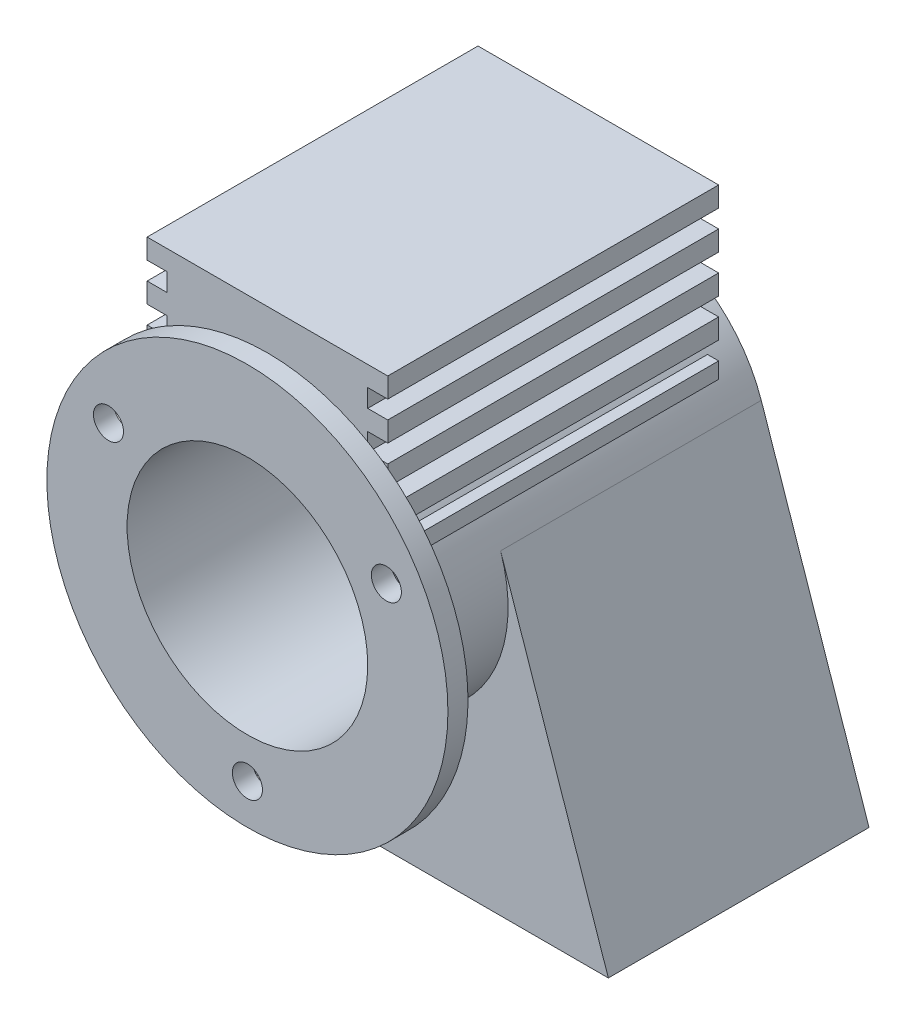
SolidWorks part; units mm, degrees
ref_plane "Front Plane" through (0, 0, 0) normal (0, 0, 1) x (1, 0, 0)
ref_plane "Top Plane" through (0, 0, 0) normal (0, 1, 0) x (1, 0, 0)
ref_plane "Right Plane" through (0, 0, 0) normal (1, 0, 0) x (0, 0, -1)
sketch "Sketch1" plane through (0, 0, 0) normal (0, 0, 1) x (1, 0, 0)
  line L0 (-6, -6.75) -> (6, -6.75)
  line L1 (-6, -6.75) -> (-3.3126, 1.1298)
  line L2 (6, -6.75) -> (3.3126, 1.1298)
  circle A0 centre (0, 0) radius 0.75
  arc A1 (3.3126, 1.1298) -> (-3.3126, 1.1298) centre (0, 0) ccw
  point P6 (0, -6.75)
  dimension "D1" = 1.5
  dimension "D2" = 7
  dimension "D3" = 12
  dimension "D4" = 6.75
extrude "Boss-Extrude1" add sketch "Sketch1" against normal blind 6.5
sketch "Sketch6" plane through (0, 0, 0) normal (0, 0, 1) x (1, 0, 0)
  circle A0 centre (0, 0) radius 3.5
  dimension "D1" = 7
extrude "Boss-Extrude4" add sketch "Sketch6" along normal blind 2.5
sketch "Sketch7" plane through (0, 0, 2.5) normal (0, 0, 1) x (1, 0, 0)
  circle A0 centre (0, 0) radius 5
  dimension "D1" = 10
extrude "Boss-Extrude5" add sketch "Sketch7" along normal blind 0.5
sketch "Sketch8" plane through (0, 0, 3) normal (0, 0, 1) x (1, 0, 0)
  circle A0 centre (0, 0) radius 0.75
  dimension "D1" = 1.5
extrude "Cut-Extrude1" cut sketch "Sketch8" against normal up to surface (3 mm away) up to face at (0, -3.9676, 0)
sketch "Sketch10" plane through (0, 0, 0) normal (0, 0, 1) x (1, 0, 0)
  line L1 (-3, 6) -> (3, 6)
  line L2 (-3, 6) -> (-3, 5.5)
  line L3 (-3, 1.7) -> (3, 1.7)
  line L4 (3, 6) -> (3, 5.5)
  line L8 (-3, 5.05) -> (-3, 4.55)
  line L9 (-3, 5.5) -> (-2.5, 5.5)
  line L10 (-3, 5.05) -> (-2.5, 5.05)
  line L11 (-2.5, 5.5) -> (-2.5, 5.05)
  line L12 (-3, 4.1) -> (-3, 3.6)
  line L13 (-3, 4.55) -> (-2.5, 4.55)
  line L14 (-3, 4.1) -> (-2.5, 4.1)
  line L15 (-2.5, 4.55) -> (-2.5, 4.1)
  line L16 (-3, 3.15) -> (-3, 2.65)
  line L17 (-3, 3.6) -> (-2.5, 3.6)
  line L18 (-3, 3.15) -> (-2.5, 3.15)
  line L19 (-2.5, 3.6) -> (-2.5, 3.15)
  line L20 (3, 5.05) -> (3, 4.55)
  line L21 (3, 5.5) -> (2.5, 5.5)
  line L22 (3, 5.05) -> (2.5, 5.05)
  line L23 (2.5, 5.5) -> (2.5, 5.05)
  line L24 (3, 4.1) -> (3, 3.6)
  line L25 (3, 4.55) -> (2.5, 4.55)
  line L26 (3, 4.1) -> (2.5, 4.1)
  line L27 (2.5, 4.55) -> (2.5, 4.1)
  line L28 (3, 3.15) -> (3, 2.65)
  line L29 (3, 3.6) -> (2.5, 3.6)
  line L30 (3, 3.15) -> (2.5, 3.15)
  line L31 (2.5, 3.6) -> (2.5, 3.15)
  line L32 (-3, 2.2) -> (-3, 1.7)
  line L33 (-3, 2.2) -> (-2.5, 2.2)
  line L34 (-3, 2.65) -> (-2.5, 2.65)
  line L35 (-2.5, 2.2) -> (-2.5, 2.65)
  line L36 (3, 2.2) -> (3, 1.7)
  line L37 (3, 2.65) -> (2.5, 2.65)
  line L38 (3, 2.2) -> (2.5, 2.2)
  line L39 (2.5, 2.65) -> (2.5, 2.2)
  point P4 (0, 1.7)
  point P5 (2.4988, 1.9984)
  dimension "D1" = 6
  dimension "D2" = 6
  dimension "D3" = 0.45
  dimension "D4" = 0.5
  dimension "D5" = 0.95
  dimension "D7" = 0.5
extrude "Boss-Extrude6" add sketch "Sketch10" against normal blind 8.25 from surface at 2.5 starting at face at (3.5, 0, 2.5)
sketch "Sketch11" plane through (0, 0, 3) normal (0, 0, 1) x (1, 0, 0)
  line L0 (0, 0) -> (7.7874, 0) construction
  line L1 (0, 0) -> (6.5011, 3.7534) construction
  circle A0 centre (0, 0) radius 4 construction
  circle A1 centre (3.4641, 2) radius 0.375
  circle A2 centre (0, -4) radius 0.375
  circle A3 centre (-3.4641, 2) radius 0.375
  point P8 (0, 0)
  point P9 (0, 0)
  point P13 (0, 0)
  dimension "D2" = 8
  dimension "D3" = 0.75
  dimension "D1" = 30
  dimension "D4" = 3
extrude "Cut-Extrude2" cut sketch "Sketch11" against normal up to next
sketch "Sketch13" plane through (0, 0, 0) normal (0, 0, 1) x (1, 0, 0)
  circle A0 centre (0, 0) radius 3
  dimension "D1" = 6
extrude "Cut-Extrude3" cut sketch "Sketch13" against normal blind 8.5 from surface at 3 starting at face at (3.8391, 2, 3)
